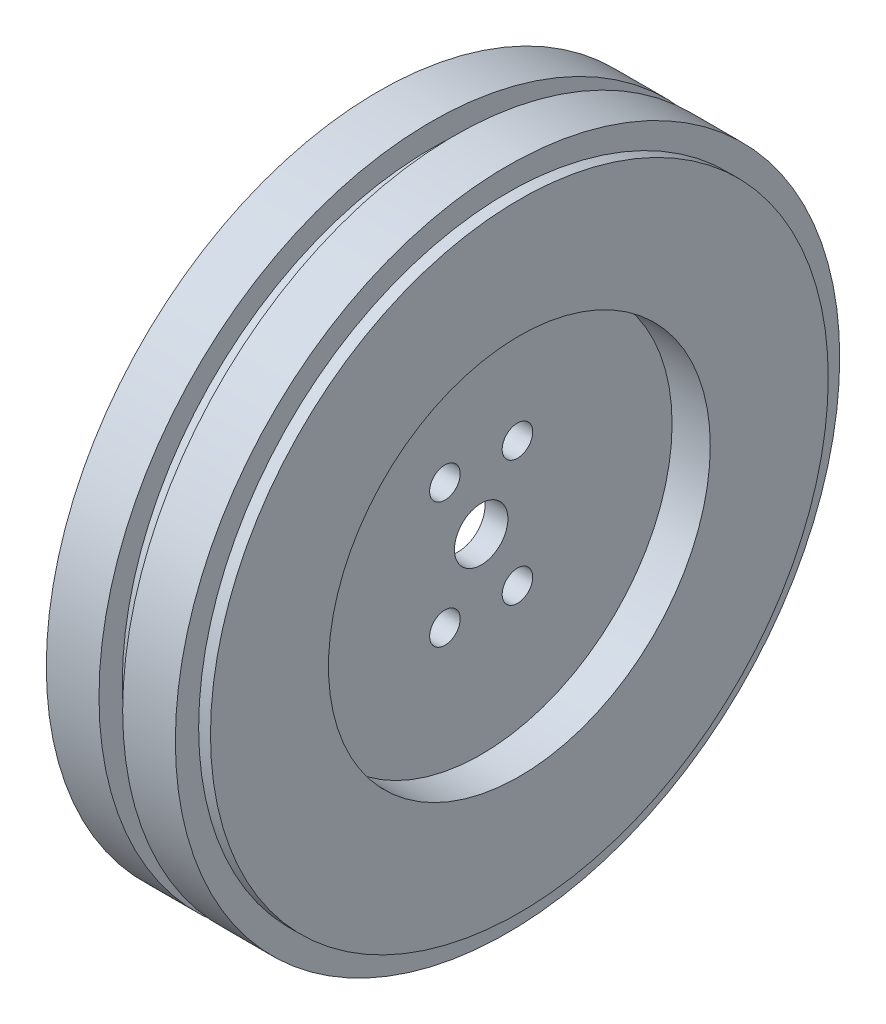
SolidWorks part; units mm, degrees
ref_plane "Plan de face" through (0, 0, 0) normal (0, 0, 1) x (1, 0, 0)
ref_plane "Plan de dessus" through (0, 0, 0) normal (0, 1, 0) x (1, 0, 0)
ref_plane "Plan de droite" through (0, 0, 0) normal (1, 0, 0) x (0, 0, -1)
sketch "Esquisse1" plane through (0, 0, 0) normal (0, 0, 1) x (1, 0, 0)
  line L0 (-49.6445, 0) -> (53.9199, 0) construction
  line L1 (0, 34) -> (0, 0)
  line L2 (0, 34) -> (-32, 34)
  line L3 (-32, 34) -> (-32, 40)
  line L4 (-32, 40) -> (-27, 40)
  line L5 (-27, 40) -> (-27, 39)
  line L6 (-27, 39) -> (3, 39)
  line L7 (3, 39) -> (3, 40)
  line L8 (3, 40) -> (8, 40)
  line L9 (8, 40) -> (8, 0)
  line L13 (0, 0) -> (8, 0)
  dimension "D2" = 5
  dimension "D3" = 5
  dimension "D4" = 40
  dimension "D5" = 1
  dimension "D6" = 8
  dimension "D10" = 6
  dimension "D11" = 1
  dimension "D12" = 30
revolve "Révolution1" add sketch "Esquisse1" angle 360 about L0
sketch "Esquisse2" plane through (0, 0, 0) normal (0, 0, 1) x (1, 0, 0)
  line L3 (0, 0) -> (8, 0) construction
  line L11 (8, -40) -> (8, 40) construction
  line L12 (8, 0) -> (8, 12.5)
  line L13 (8, 12.5) -> (3, 12.5)
  line L14 (3, 12.5) -> (3, 0)
  line L15 (3, 0) -> (8, 0)
  dimension "D1" = 25
  dimension "D2" = 5
revolve "Enlèvement de matière-Révolution1" cut sketch "Esquisse2" angle 360 about L3
sketch "Esquisse3" plane through (3, 0, 0) normal (1, 0, 0) x (0, 0, -1)
  line L0 (0, 12.5) -> (0, 0) construction
  line L1 (0, 0) -> (12.5, 0) construction
  line L2 (4.75, 8.2272) -> (0, 0) construction
  circle A0 centre (4.75, 8.2272) radius 2
  circle A2 centre (0, 0) radius 12.5 construction
  circle A3 centre (0, 0) radius 12.5 construction
  circle A4 centre (-4.75, 8.2272) radius 2
  circle A5 centre (4.75, -8.2272) radius 2
  circle A6 centre (-4.75, -8.2272) radius 2
  dimension "D1" = 4
  dimension "D2" = 9.5
  dimension "D3" = 30
extrude "Enlèv. mat.-Extru.1" cut sketch "Esquisse3" against normal through all
sketch "Esquisse4" plane through (3, 0, 0) normal (1, 0, 0) x (0, 0, -1)
  circle A0 centre (0, 0) radius 3.5
  dimension "D1" = 7
extrude "Enlèv. mat.-Extru.2" cut sketch "Esquisse4" against normal through all
sketch "Sketch1" plane through (-32, 0, 0) normal (-1, 0, 0) x (0, 0, 1)
  circle A1 centre (0, 0) radius 40
  circle A2 centre (0, 0) radius 40
  dimension "D1" = 0
extrude "Cut-Extrude1" cut sketch "Sketch1" against normal blind 20
sketch "Sketch2" plane through (3, 0, 0) normal (-1, 0, 0) x (0, 0, 1)
  circle A0 centre (0, 0) radius 39 construction
  circle A1 centre (0, 0) radius 40
  circle A2 centre (0, 0) radius 40
  circle A3 centre (0, 0) radius 39
  dimension "D1" = 0
extrude "Boss-Extrude2" add sketch "Sketch2" along normal blind 15
sketch "Sketch3" plane through (8, 0, 0) normal (1, 0, 0) x (0, 0, -1)
  circle A0 centre (0, 0) radius 25
  dimension "D1" = 50
extrude "Cut-Extrude2" cut sketch "Sketch3" against normal blind 5
sketch "Sketch4" plane through (-12, 0, 0) normal (-1, 0, 0) x (0, 0, 1)
  circle A0 centre (0, 0) radius 43.5
  circle A1 centre (0, 0) radius 40 construction
  circle A2 centre (0, 0) radius 40
  dimension "D1" = 87
extrude "Boss-Extrude3" add sketch "Sketch4" against normal blind 20
sketch "Sketch5" plane through (-12, 0, 0) normal (-1, 0, 0) x (0, 0, 1)
  circle A0 centre (0, 0) radius 43.5
  circle A1 centre (0, 0) radius 40.45
  dimension "D1" = 87
  dimension "D2" = 80.9
extrude "Cut-Extrude3" cut sketch "Sketch5" against normal blind 1.55
ref_plane "Plane1" through (-2, 0, 0) normal (-1, 0, 0) x (0, 0, 1)
sketch "Sketch6" plane through (-2, 0, 0) normal (-1, 0, 0) x (0, 0, 1)
  circle A0 centre (0, 0) radius 40.45 construction
  circle A1 centre (0, 0) radius 43.5
  circle A2 centre (0, 0) radius 43.5
  circle A3 centre (0, 0) radius 40.45
  dimension "D1" = 0
extrude "Cut-Extrude4" cut sketch "Sketch6" against normal blind 1.55 and the other way blind 1.55
sketch "Sketch7" plane through (8, 0, 0) normal (1, 0, 0) x (0, 0, -1)
  circle A0 centre (0, 0) radius 40.45 construction
  circle A1 centre (0, 0) radius 40.45
  circle A2 centre (0, 0) radius 43.5 construction
  circle A3 centre (0, 0) radius 43.5
extrude "Cut-Extrude5" cut sketch "Sketch7" against normal blind 1.55
